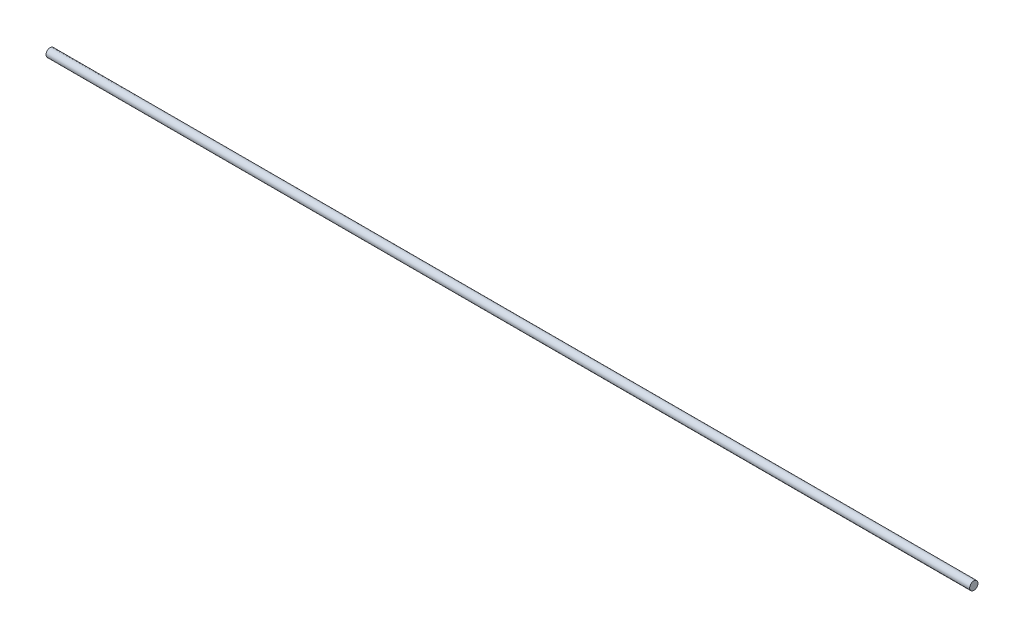
SolidWorks part; units mm, degrees
ref_plane "Front Plane" through (0, 0, 0) normal (0, 0, 1) x (1, 0, 0)
ref_plane "Top Plane" through (0, 0, 0) normal (0, 1, 0) x (1, 0, 0)
ref_plane "Right Plane" through (0, 0, 0) normal (1, 0, 0) x (0, 0, -1)
sketch "Sketch12" plane through (0, 0, 0) normal (1, 0, 0) x (0, 0, -1)
  circle A0 centre (0, 0) radius 0.45
  dimension "D1" = 0.9
extrude "Boss-Extrude9" add sketch "Sketch12" along normal blind 100 separate body
